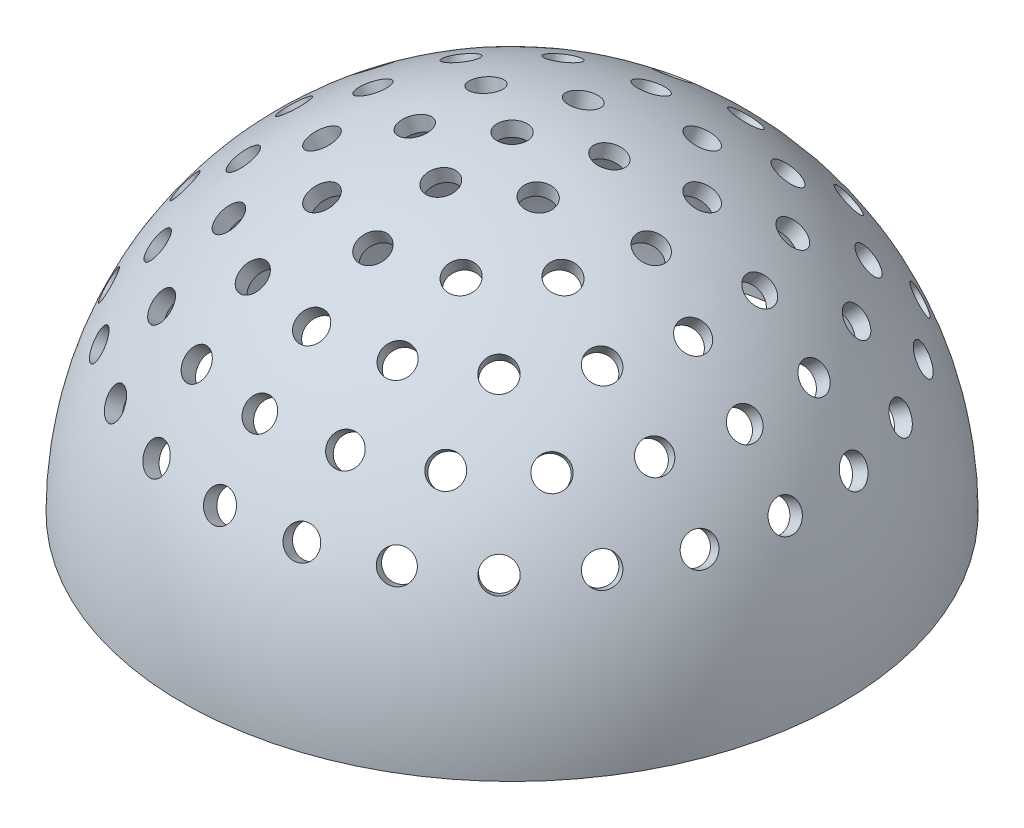
SolidWorks part; units mm, degrees
ref_plane "Front Plane" through (0, 0, 0) normal (0, 0, 1) x (1, 0, 0)
ref_plane "Top Plane" through (0, 0, 0) normal (0, 1, 0) x (1, 0, 0)
ref_plane "Right Plane" through (0, 0, 0) normal (1, 0, 0) x (0, 0, -1)
sketch "Sketch1" plane through (0, 0, 0) normal (0, 0, 1) x (1, 0, 0)
  line L0 (0, 0) -> (0, 11)
  line L1 (0, 0) -> (11, 0)
  arc A0 (0, 11) -> (11, 0) centre (0, 0) cw
  dimension "D1" = 11
  dimension "D2" = 11
revolve "Revolve1" add sketch "Sketch1" angle 360 about L0
sketch "Sketch2" plane through (0, 0, 0) normal (0, 0, 1) x (1, 0, 0)
  line L0 (0, 0) -> (0, 10.5)
  line L1 (0, 0) -> (10.5, 0)
  line L2 (-11, 0) -> (11, 0) construction
  arc A0 (0, 10.5) -> (10.5, 0) centre (0, 0) cw
  dimension "D1" = 10.5
  dimension "D2" = 10.5
revolve "Cut-Revolve1" cut sketch "Sketch2" angle 360 about L0
sketch "Sketch3" plane through (0, 0, 0) normal (0, 1, 0) x (1, 0, 0)
  circle A0 centre (0, 0) radius 0.5
  dimension "D1" = 1
extrude "Cut-Extrude1" cut sketch "Sketch3" along normal through all
pattern_circular "CirPattern1" count 2 every 12.5 about axis through (0, 0, 0) along (1, 0, 0) of "Cut-Extrude1"
pattern_circular "CirPattern2" count 6 over 360 about axis through (0, 0, 0) along (0, 1, 0) of "CirPattern1"
pattern_circular "CirPattern3" count 2 every 25 about axis through (0, 0, 0) along (1, 0, 0) of "Cut-Extrude1"
pattern_circular "CirPattern4" count 2 every 37.5 about axis through (0, 0, 0) along (1, 0, 0) of "Cut-Extrude1"
pattern_circular "CirPattern5" count 2 every 50 about axis through (0, 0, 0) along (1, 0, 0) of "Cut-Extrude1"
pattern_circular "CirPattern6" count 2 every 62.5 about axis through (0, 0, 0) along (1, 0, 0) of "Cut-Extrude1"
pattern_circular "CirPattern7" count 12 over 360 about axis through (0, 0, 0) along (0, 1, 0) of "CirPattern3"
pattern_circular "CirPattern8" count 17 over 360 about axis through (0, 0, 0) along (0, 1, 0) of "CirPattern4"
pattern_circular "CirPattern9" count 21 over 360 about axis through (0, 0, 0) along (0, 1, 0) of "CirPattern5"
pattern_circular "CirPattern10" count 25 over 360 about axis through (0, 0, 0) along (0, 1, 0) of "CirPattern6"
equation "\"D1@Sketch1\"=\"dia_inner_out\""
equation "\"D2@Sketch1\"=\"dia_inner_out\""
equation "\"D1@Sketch2\"=\"dia_inner_in\""
equation "\"D2@Sketch2\"=\"dia_inner_in\""
equation "\"D1@Sketch3\"=\"d_marker\""
equation "\"D2@CirPattern1\"=\"degrees\""
equation "\"D1@CirPattern2\"=\"n_markers_1\""
equation "\"D2@CirPattern3\"=2*\"degrees\""
equation "\"D2@CirPattern4\"=3*\"degrees\""
equation "\"D2@CirPattern5\"=4*\"degrees\""
equation "\"D2@CirPattern6\"=5*\"degrees\""
equation "\"D1@CirPattern7\"=\"n_markers_2\""
equation "\"D1@CirPattern10\"=\"n_markers_5\""
equation "\"D1@CirPattern8\"=\"n_markers_3\""
equation "\"D1@CirPattern9\"=\"n_markers_4\""
equation "\"dia_difflayer\"= 13"
equation "\"dia_outer_out\"= 12.5"
equation "\"dia_outer_in\"= 12"
equation "\"dia_inner_out\"= 11"
equation "\"dia_inner_in\"= 10.5"
equation "\"degrees\"= 12.5"
equation "\"d_marker\"= 1"
equation "\"t_marker\"= 0.5"
equation "\"n_markers_1\"= 6"
equation "\"n_markers_2\"= round ( 6 * sin ( 2*\"degrees\" ) / sin ( \"degrees\" ) )"
equation "\"n_markers_3\"= round ( 6 * sin ( 3*\"degrees\" ) / sin ( \"degrees\" ) )"
equation "\"n_markers_4\"= round ( 6 * sin ( 4*\"degrees\" ) / sin ( \"degrees\" ) )"
equation "\"n_markers_5\"= round ( 6 * sin ( 5*\"degrees\" ) / sin ( \"degrees\" ) )"
equation "\"n_teeth\"= 8"
